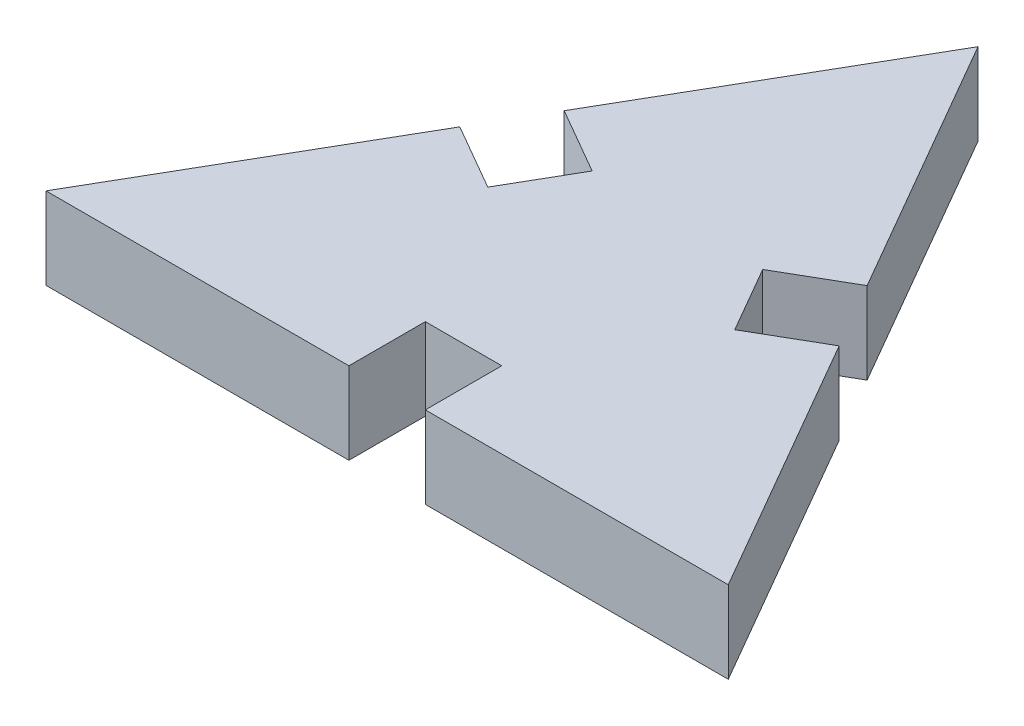
SolidWorks part; units mm, degrees
material "Beech"
ref_plane "Front Plane" through (0, 0, 0) normal (0, 0, 1) x (1, 0, 0)
ref_plane "Top Plane" through (0, 0, 0) normal (0, 1, 0) x (1, 0, 0)
ref_plane "Right Plane" through (0, 0, 0) normal (1, 0, 0) x (0, 0, -1)
sketch "Sketch1" plane through (0, 0, 0) normal (0, 1, 0) x (1, 0, 0)
  line L0 (0, 14.4338) -> (-12.5, -7.2169)
  line L1 (-12.5, -7.2169) -> (12.5, -7.2169)
  line L2 (12.5, -7.2169) -> (0, 14.4338)
  line L3 (-6.25, 3.6084) -> (12.5, -7.2169) construction
  line L4 (-12.5, -7.2169) -> (6.25, 3.6084) construction
  point P2 (0, 0)
  dimension "D1" = 25
extrude "Boss-Extrude1" add sketch "Sketch1" along normal blind 3
sketch "Sketch3" plane through (0, 3, 0) normal (0, 1, 0) x (1, 0, 0)
  line L0 (-6.25, 3.6084) -> (12.5, -7.2169) construction
  line L1 (0, 14.4338) -> (-12.5, -7.2169) construction
  line L2 (6.95, 2.396) -> (4.5251, 0.996)
  line L4 (3.1251, 3.4209) -> (4.5251, 0.996)
  line L6 (-6.95, 2.396) -> (-4.5251, 0.996)
  line L7 (-4.5251, 0.996) -> (-3.1251, 3.4209)
  line L8 (-5.55, 4.8209) -> (-3.1251, 3.4209)
  line L15 (-6.95, 2.396) -> (-5.55, 4.8209)
  line L18 (5.55, 4.8209) -> (3.1251, 3.4209)
  line L19 (5.55, 4.8209) -> (6.95, 2.396)
  line L20 (-1.4, -7.2169) -> (-1.4, -4.4169)
  line L21 (1.4, -4.4169) -> (-1.4, -4.4169)
  line L22 (1.4, -7.2169) -> (1.4, -4.4169)
  line L23 (1.4, -7.2169) -> (-1.4, -7.2169)
  point P20 (-3.8251, 2.2084)
  point P22 (0, 0)
  dimension "D2" = 2.8
  dimension "D3" = 3
extrude "Cut-Extrude1" cut sketch "Sketch3" against normal up to next
sketch "Sketch4" plane through (0, 3, 0) normal (0, 1, 0) x (1, 0, 0)
  line L0 (0, 14.4338) -> (0, -4.4169) construction
  line L1 (1.4, -7.2169) -> (12.5, -7.2169) construction
  line L2 (-5, -0.9669) -> (5, -0.9669) construction
  line L5 (1.4, -4.4169) -> (-1.4, -4.4169) construction
  point P9 (0, -0.9669)
  dimension "D2" = 10
  dimension "D1" = 6.25
equation "\"D1@Boss-Extrude1\"=\"T@d20.Assembly\""
equation "\"D2@Sketch3\"=\"T@d20.Assembly\"-0.2"
equation "\"text_position\"= \"size\" * 0.25"
equation "\"D1@Sketch4\"=\"text_position\""
equation "\"size\"= \"size@d20.Assembly\""
equation "\"D1@Sketch1\"=\"size\""
